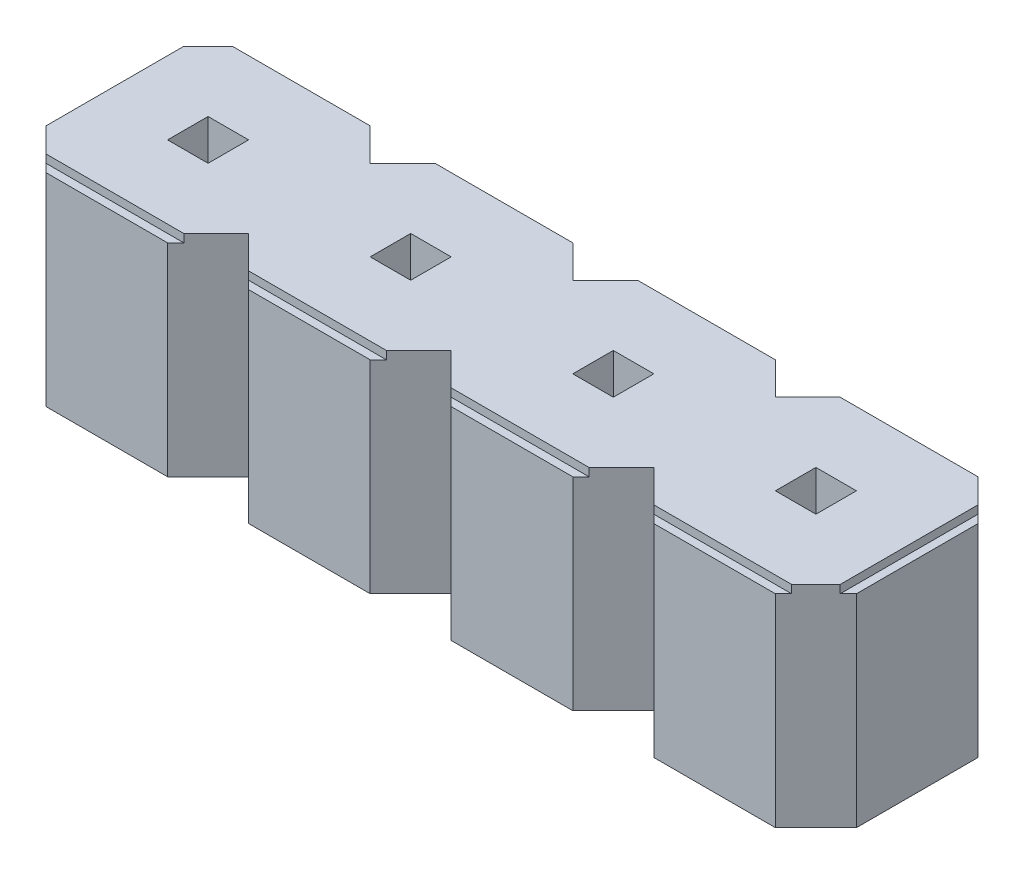
SolidWorks part; units mm, degrees
ref_plane "Front Plane" through (0, 0, 0) normal (0, 0, 1) x (1, 0, 0)
ref_plane "Top Plane" through (0, 0, 0) normal (0, 1, 0) x (1, 0, 0)
ref_plane "Right Plane" through (0, 0, 0) normal (1, 0, 0) x (0, 0, -1)
sketch "Sketch1" plane through (0, 0, 0) normal (0, 1, 0) x (1, 0, 0)
  line L0 (-1.25, 0.75) -> (-0.75, 1.25)
  line L1 (-0.75, -1.25) -> (0.75, -1.25)
  line L2 (-1.25, -0.75) -> (-1.25, 0.75)
  line L3 (-0.75, 1.25) -> (0.75, 1.25)
  line L5 (-1.25, -1.25) -> (-1, -1) construction
  line L6 (-1.25, 1.25) -> (-1, 1) construction
  line L7 (0.75, 1.25) -> (1.25, 0.75)
  line L8 (0.75, -1.25) -> (1.25, -0.75)
  line L9 (-1.25, -0.75) -> (-0.75, -1.25)
  line L10 (1.75, 1.25) -> (3.25, 1.25)
  line L12 (3.25, 1.25) -> (3.75, 0.75)
  line L13 (1.25, 0.75) -> (1.75, 1.25)
  line L15 (1.25, -0.75) -> (1.75, -1.25)
  line L16 (1.75, -1.25) -> (3.25, -1.25)
  line L17 (3.25, -1.25) -> (3.75, -0.75)
  line L18 (4.25, 1.25) -> (5.75, 1.25)
  line L20 (5.75, 1.25) -> (6.25, 0.75)
  line L21 (3.75, 0.75) -> (4.25, 1.25)
  line L23 (3.75, -0.75) -> (4.25, -1.25)
  line L24 (4.25, -1.25) -> (5.75, -1.25)
  line L25 (5.75, -1.25) -> (6.25, -0.75)
  line L26 (6.75, 1.25) -> (8.25, 1.25)
  line L27 (8.75, -0.75) -> (8.75, 0.75)
  line L28 (8.25, 1.25) -> (8.75, 0.75)
  line L29 (6.25, 0.75) -> (6.75, 1.25)
  line L31 (6.25, -0.75) -> (6.75, -1.25)
  line L32 (6.75, -1.25) -> (8.25, -1.25)
  line L33 (8.25, -1.25) -> (8.75, -0.75)
  line L34 (1.25, -0.75) -> (1.25, 0.75) [skipped]
  line L35 (3.75, -0.75) -> (3.75, 0.75) [skipped]
  line L36 (6.25, -0.75) -> (6.25, 0.75) [skipped]
  line L37 (1, 1) -> (1.25, 1.25) construction
  line L38 (1, -1) -> (1.25, -1.25) construction
  line L39 (2.25, 0.25) -> (2.75, 0.25) construction
  line L40 (-0.25, -0.25) -> (0.25, -0.25) construction
  line L41 (-0.25, -0.25) -> (-0.25, 0.25) construction
  line L42 (-0.25, 0.25) -> (0.25, 0.25) construction
  line L43 (0.25, -0.25) -> (0.25, 0.25) construction
  line L44 (-0.25, -0.25) -> (0.25, 0.25) construction
  line L45 (-0.25, 0.25) -> (0.25, -0.25) construction
  line L46 (2.75, -0.25) -> (2.75, 0.25) construction
  line L47 (2.25, -0.25) -> (2.75, -0.25) construction
  line L48 (2.25, -0.25) -> (2.25, 0.25) construction
  line L49 (4.75, 0.25) -> (5.25, 0.25) construction
  line L50 (5.25, -0.25) -> (5.25, 0.25) construction
  line L51 (4.75, -0.25) -> (5.25, -0.25) construction
  line L52 (4.75, -0.25) -> (4.75, 0.25) construction
  line L53 (7.25, 0.25) -> (7.75, 0.25) construction
  line L54 (7.75, -0.25) -> (7.75, 0.25) construction
  line L55 (7.25, -0.25) -> (7.75, -0.25) construction
  line L56 (7.25, -0.25) -> (7.25, 0.25) construction
  line L57 (-1.25, -0.75) -> (1.25, -0.75)
  line L58 (3.75, -0.75) -> (6.25, -0.75)
  line L59 (8.75, -0.75) -> (6.25, -0.75)
  point P0 (0, 0)
  point P14 (0, 0)
  point P47 (2.5, 0.25)
  point P48 (2.5, 1.25)
  dimension "D1" = 2.5
  dimension "D2" = 4
  dimension "D3" = 0.5
  dimension "D9" = 2.5
  dimension "D8" = 4
extrude "Boss-Extrude1" add sketch "Sketch1" along normal mid plane 2.6 contours L58 L23 L24 L25 | L33 L59 L31 L32 | L59 L27 L28 L26 L29 L20 L18 L21 L12 L10 L13 L7 L3 L0 L2 L57 L15 L16 L17 L58 | L57 L9 L1 L8
sketch "Sketch2" plane through (0, 1.3, 0) normal (0, 1, 0) x (1, 0, 0)
  line L0 (3.75, 0.75) -> (3.75, -0.75) construction
  line L2 (-1.15, -1.15) -> (8.65, -1.15)
  line L3 (-1.15, -1.15) -> (-1.15, 1.15)
  line L4 (-1.15, 1.15) -> (8.65, 1.15)
  line L5 (8.65, -1.15) -> (8.65, 1.15)
  line L6 (-1.15, -1.15) -> (8.65, 1.15) construction
  line L7 (-1.15, 1.15) -> (8.65, -1.15) construction
  line L8 (-2.0486, -2.0847) -> (9.5486, -2.0847)
  line L9 (-2.0486, -2.0847) -> (-2.0486, 2.0847)
  line L10 (-2.0486, 2.0847) -> (9.5486, 2.0847)
  line L11 (9.5486, -2.0847) -> (9.5486, 2.0847)
  line L12 (-2.0486, -2.0847) -> (9.5486, 2.0847) construction
  line L13 (-2.0486, 2.0847) -> (9.5486, -2.0847) construction
  point P4 (3.75, 0)
  point P9 (3.75, 0)
  dimension "D1" = 9.8
  dimension "D2" = 2.3
extrude "Cut-Extrude1" cut sketch "Sketch2" against normal blind 0.1
sketch "Sketch3" plane through (0, 1.3, 0) normal (0, 1, 0) x (1, 0, 0)
  line L0 (2.25, 0.25) -> (2.75, 0.25)
  line L1 (-0.25, -0.25) -> (0.25, -0.25)
  line L2 (-0.25, -0.25) -> (-0.25, 0.25)
  line L3 (-0.25, 0.25) -> (0.25, 0.25)
  line L4 (0.25, -0.25) -> (0.25, 0.25)
  line L5 (-0.25, -0.25) -> (0.25, 0.25) construction
  line L6 (-0.25, 0.25) -> (0.25, -0.25) construction
  line L7 (2.75, -0.25) -> (2.75, 0.25)
  line L8 (2.25, -0.25) -> (2.25, 0.25)
  line L9 (2.25, -0.25) -> (2.75, -0.25)
  line L10 (4.75, 0.25) -> (5.25, 0.25)
  line L11 (5.25, -0.25) -> (5.25, 0.25)
  line L12 (4.75, -0.25) -> (4.75, 0.25)
  line L13 (4.75, -0.25) -> (5.25, -0.25)
  line L14 (7.25, 0.25) -> (7.75, 0.25)
  line L15 (7.75, -0.25) -> (7.75, 0.25)
  line L16 (7.25, -0.25) -> (7.25, 0.25)
  line L17 (7.25, -0.25) -> (7.75, -0.25)
  point P0 (0, 0)
  dimension "D1" = 0.5
  dimension "D2" = 0.5
  dimension "D3" = 4
extrude "Cut-Extrude2" cut sketch "Sketch3" against normal through all
